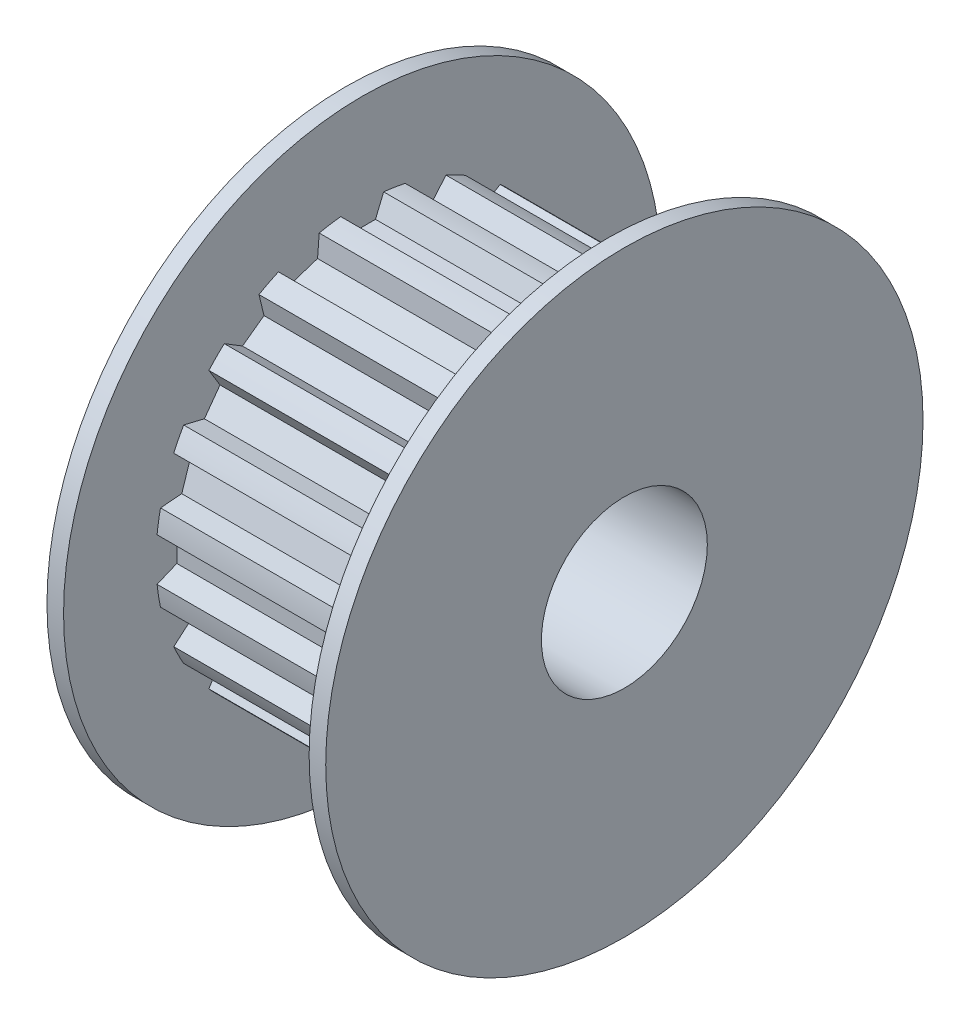
SolidWorks part; units mm, degrees
ref_plane "Front Plane" through (0, 0, 0) normal (0, 0, 1) x (1, 0, 0)
ref_plane "Top Plane" through (0, 0, 0) normal (0, 1, 0) x (1, 0, 0)
ref_plane "Right Plane" through (0, 0, 0) normal (1, 0, 0) x (0, 0, -1)
ref_plane "Plane1" through (0, 0, 0) normal (0, 0, -1) x (-1, 0, 0)
sketch "Sketch1" plane through (0, 0, 0) normal (0, 0, -1) x (-1, 0, 0)
  line L0 (-7.9, 9) -> (-7.9, 0)
  line L1 (-7.9, 0) -> (-7.4, 0)
  line L2 (-7.4, 0) -> (-7.4, 9)
  line L3 (-7.4, 9) -> (-7.9, 9)
  line L4 (-7.9, 0) -> (-7.4, 0) construction
revolve "Revolve1" add sketch "Sketch1" angle 360 about L4
sketch "Sketch2" plane through (7.4, 0, 0) normal (-1, 0, 0) x (0, 0, 1)
  line L0 (6.0784, -1.2957) -> (5.4374, -1.3461)
  line L1 (5.4374, -1.3461) -> (5.1902, -2.107)
  line L2 (5.1902, -2.107) -> (5.6791, -2.5246)
  line L3 (5.3806, -3.1106) -> (4.7553, -2.9605)
  line L4 (4.7553, -2.9605) -> (4.2851, -3.6077)
  line L5 (4.2851, -3.6077) -> (4.621, -4.156)
  line L6 (4.156, -4.621) -> (3.6077, -4.2851)
  line L7 (3.6077, -4.2851) -> (2.9605, -4.7553)
  line L8 (2.9605, -4.7553) -> (3.1106, -5.3806)
  line L9 (2.5246, -5.6791) -> (2.107, -5.1902)
  line L10 (2.107, -5.1902) -> (1.3461, -5.4374)
  line L11 (1.3461, -5.4374) -> (1.2957, -6.0784)
  line L12 (0.6461, -6.1813) -> (0.4, -5.5872)
  line L13 (0.4, -5.5872) -> (-0.4, -5.5872)
  line L14 (-0.4, -5.5872) -> (-0.6461, -6.1813)
  line L15 (-1.2957, -6.0784) -> (-1.3461, -5.4374)
  line L16 (-1.3461, -5.4374) -> (-2.107, -5.1902)
  line L17 (-2.107, -5.1902) -> (-2.5246, -5.6791)
  line L18 (-3.1106, -5.3806) -> (-2.9605, -4.7553)
  line L19 (-2.9605, -4.7553) -> (-3.6077, -4.2851)
  line L20 (-3.6077, -4.2851) -> (-4.156, -4.621)
  line L21 (-4.621, -4.156) -> (-4.2851, -3.6077)
  line L22 (-4.2851, -3.6077) -> (-4.7553, -2.9605)
  line L23 (-4.7553, -2.9605) -> (-5.3806, -3.1106)
  line L24 (-5.6791, -2.5246) -> (-5.1902, -2.107)
  line L25 (-5.1902, -2.107) -> (-5.4374, -1.3461)
  line L26 (-5.4374, -1.3461) -> (-6.0784, -1.2957)
  line L27 (-6.1813, -0.6461) -> (-5.5872, -0.4)
  line L28 (-5.5872, -0.4) -> (-5.5872, 0.4)
  line L29 (-5.5872, 0.4) -> (-6.1813, 0.6461)
  line L30 (-6.0784, 1.2957) -> (-5.4374, 1.3461)
  line L31 (-5.4374, 1.3461) -> (-5.1902, 2.107)
  line L32 (-5.1902, 2.107) -> (-5.6791, 2.5246)
  line L33 (-5.3806, 3.1106) -> (-4.7553, 2.9605)
  line L34 (-4.7553, 2.9605) -> (-4.2851, 3.6077)
  line L35 (-4.2851, 3.6077) -> (-4.621, 4.156)
  line L36 (-4.156, 4.621) -> (-3.6077, 4.2851)
  line L37 (-3.6077, 4.2851) -> (-2.9605, 4.7553)
  line L38 (-2.9605, 4.7553) -> (-3.1106, 5.3806)
  line L39 (-2.5246, 5.6791) -> (-2.107, 5.1902)
  line L40 (-2.107, 5.1902) -> (-1.3461, 5.4374)
  line L41 (-1.3461, 5.4374) -> (-1.2957, 6.0784)
  line L42 (-0.6461, 6.1813) -> (-0.4, 5.5872)
  line L43 (-0.4, 5.5872) -> (0.4, 5.5872)
  line L44 (0.4, 5.5872) -> (0.6461, 6.1813)
  line L45 (1.2957, 6.0784) -> (1.3461, 5.4374)
  line L46 (1.3461, 5.4374) -> (2.107, 5.1902)
  line L47 (2.107, 5.1902) -> (2.5246, 5.6791)
  line L48 (3.1106, 5.3806) -> (2.9605, 4.7553)
  line L49 (2.9605, 4.7553) -> (3.6077, 4.2851)
  line L50 (3.6077, 4.2851) -> (4.156, 4.621)
  line L51 (4.621, 4.156) -> (4.2851, 3.6077)
  line L52 (4.2851, 3.6077) -> (4.7553, 2.9605)
  line L53 (4.7553, 2.9605) -> (5.3806, 3.1106)
  line L54 (5.6791, 2.5246) -> (5.1902, 2.107)
  line L55 (5.1902, 2.107) -> (5.4374, 1.3461)
  line L56 (5.4374, 1.3461) -> (6.0784, 1.2957)
  line L57 (6.1813, 0.6461) -> (5.5872, 0.4)
  line L58 (5.5872, 0.4) -> (5.5872, -0.4)
  line L59 (5.5872, -0.4) -> (6.1813, -0.6461)
  arc A0 (5.6791, -2.5246) -> (5.3806, -3.1106) centre (0, 0) cw
  arc A1 (4.621, -4.156) -> (4.156, -4.621) centre (0, 0) cw
  arc A2 (3.1106, -5.3806) -> (2.5246, -5.6791) centre (0, 0) cw
  arc A3 (1.2957, -6.0784) -> (0.6461, -6.1813) centre (0, 0) cw
  arc A4 (-0.6461, -6.1813) -> (-1.2957, -6.0784) centre (0, 0) cw
  arc A5 (-2.5246, -5.6791) -> (-3.1106, -5.3806) centre (0, 0) cw
  arc A6 (-4.156, -4.621) -> (-4.621, -4.156) centre (0, 0) cw
  arc A7 (-5.3806, -3.1106) -> (-5.6791, -2.5246) centre (0, 0) cw
  arc A8 (-6.0784, -1.2957) -> (-6.1813, -0.6461) centre (0, 0) cw
  arc A9 (-6.1813, 0.6461) -> (-6.0784, 1.2957) centre (0, 0) cw
  arc A10 (-5.6791, 2.5246) -> (-5.3806, 3.1106) centre (0, 0) cw
  arc A11 (-4.621, 4.156) -> (-4.156, 4.621) centre (0, 0) cw
  arc A12 (-3.1106, 5.3806) -> (-2.5246, 5.6791) centre (0, 0) cw
  arc A13 (-1.2957, 6.0784) -> (-0.6461, 6.1813) centre (0, 0) cw
  arc A14 (0.6461, 6.1813) -> (1.2957, 6.0784) centre (0, 0) cw
  arc A15 (2.5246, 5.6791) -> (3.1106, 5.3806) centre (0, 0) cw
  arc A16 (4.156, 4.621) -> (4.621, 4.156) centre (0, 0) cw
  arc A17 (5.3806, 3.1106) -> (5.6791, 2.5246) centre (0, 0) cw
  arc A18 (6.0784, 1.2957) -> (6.1813, 0.6461) centre (0, 0) cw
  arc A19 (6.1813, -0.6461) -> (6.0784, -1.2957) centre (0, 0) cw
extrude "Boss-Extrude1" add sketch "Sketch2" along normal blind 7.4
sketch "Sketch3" plane through (0, 0, 0) normal (1, 0, 0) x (0, 0, -1)
  circle A0 centre (0, 0) radius 9
extrude "Boss-Extrude2" add sketch "Sketch3" against normal blind 0.5
hole_wizard "Ø5.0 (5) Diameter Hole1" positions "Sketch5" profile "Sketch4" hole size "Ø5.0" standard "ANSI Metric"
sketch "Sketch5" plane through (7.9, 0, 0) normal (1, 0, 0) x (0, 0, -1)
  point P0 (0, 0)
sketch "Sketch4" plane through (7.9, 0, 0) normal (0, 1, 0) x (0, 0, -1)
  line L0 (0, 0) -> (0, 8.4)
  line L1 (0, 8.4) -> (2.5, 8.4)
  line L2 (2.5, 8.4) -> (2.5, 0)
  line L5 (2.5, 0) -> (0, 0)
  line L11 (0, -6.35) -> (0, 107.95) construction
  dimension "Thru Hole Dia." = 5
  dimension "Thru Hole Depth" = 8.4
